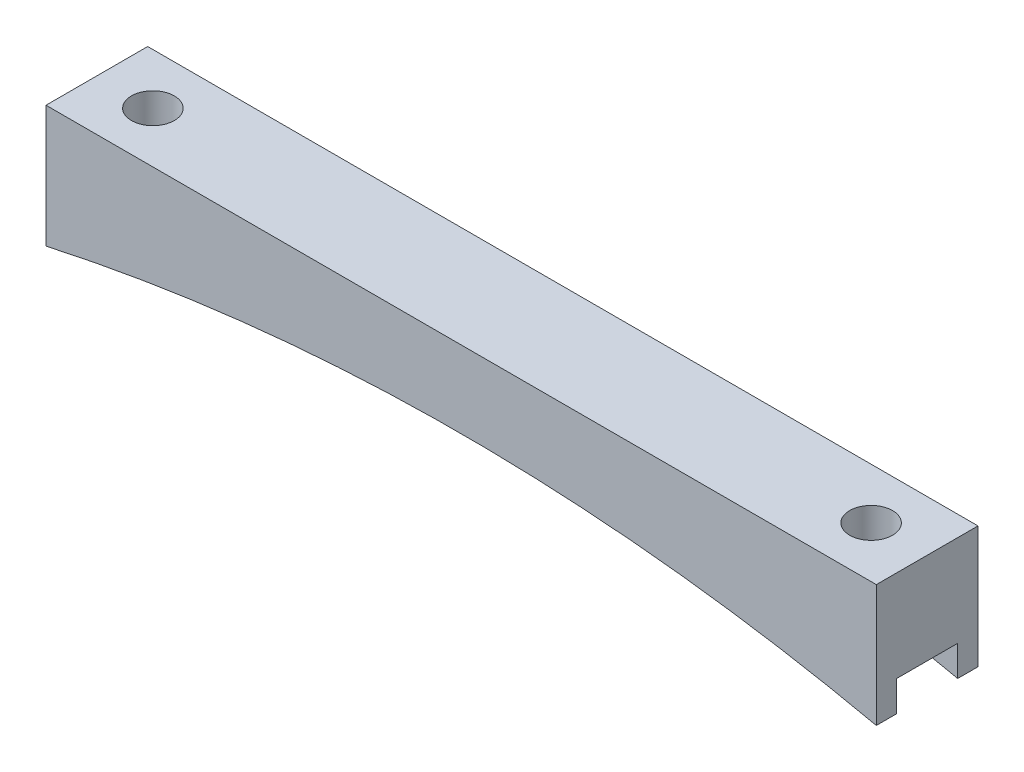
SolidWorks part; units mm, degrees
ref_plane "Front Plane" through (0, 0, 0) normal (0, 0, 1) x (1, 0, 0)
ref_plane "Top Plane" through (0, 0, 0) normal (0, 1, 0) x (1, 0, 0)
ref_plane "Right Plane" through (0, 0, 0) normal (1, 0, 0) x (0, 0, -1)
sketch "Sketch1" plane through (0, 0, 0) normal (0, 0, 1) x (1, 0, 0)
  line L0 (-51.855, 0) -> (51.855, 0)
  line L1 (-44.855, -2.54) -> (44.855, -2.54) construction
  line L2 (0, 0) -> (0, -4.6068) construction
  line L3 (51.855, 0) -> (51.855, -15.24)
  line L4 (-51.855, 0) -> (-51.855, -15.24)
  arc A0 (-51.855, -15.24) -> (51.855, -15.24) centre (0, -250.9024) cw
  point P4 (0, 0)
  point P9 (0, -2.54)
  dimension "D4" = 241.3
  dimension "D1" = 89.71
  dimension "D2" = 2.54
  dimension "D3" = 7
  dimension "D5" = 15.24
extrude "Boss-Extrude1" add sketch "Sketch1" along normal blind 12.7
sketch "Sketch2" plane through (0, 0, 0) normal (0, 1, 0) x (1, 0, 0)
  line L1 (-44.855, 0) -> (-44.855, -12.7) construction
  line L2 (-51.855, 0) -> (51.855, 0) construction
  line L3 (51.855, -12.7) -> (-51.855, -12.7) construction
  line L4 (44.855, 0) -> (44.855, -12.7) construction
  circle A0 centre (-44.855, -6.35) radius 2.675
  circle A1 centre (44.855, -6.35) radius 2.675
  circle A2 centre (-44.855, -6.35) radius 3 construction
  point P7 (-44.855, -6.35)
  dimension "D1" = 5.35
  dimension "D2" = 6
extrude "Cut-Extrude1" cut sketch "Sketch2" against normal through all
sketch "Sketch3" plane through (51.855, 0, 0) normal (1, 0, 0) x (0, 0, -1)
  line L0 (-12.7, -15.24) -> (0, -15.24) construction
  line L1 (-10.16, -15.24) -> (-2.54, -15.24)
  line L2 (-10.16, -15.24) -> (-10.16, -11.43)
  line L3 (-10.16, -11.43) -> (-2.54, -11.43)
  line L4 (-2.54, -15.24) -> (-2.54, -11.43)
  line L5 (-12.7, -15.24) -> (-12.7, 0) construction
  line L6 (0, -15.24) -> (0, 0) construction
  dimension "D1" = 2.54
  dimension "D2" = 2.54
  dimension "D3" = 3.81
extrude "Cut-Extrude2" cut sketch "Sketch3" against normal through all
